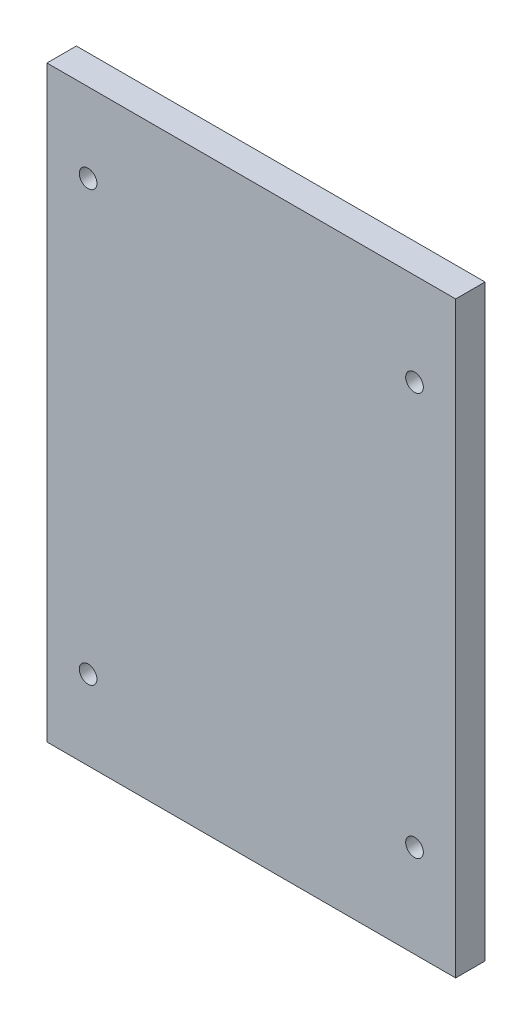
SolidWorks part; units mm, degrees
material "PBT Общее назначение"
ref_plane "Спереди" through (0, 0, 0) normal (0, 0, 1) x (1, 0, 0)
ref_plane "Сверху" through (0, 0, 0) normal (0, 1, 0) x (1, 0, 0)
ref_plane "Справа" through (0, 0, 0) normal (1, 0, 0) x (0, 0, -1)
sketch "Эскиз1" plane through (0, 0, 81) normal (0, 0, 1) x (1, 0, 0)
  line L0 (2.5, -5) -> (2.5, 95)
  line L1 (-67, -5) -> (-67, 95)
  line L4 (0, 5) -> (0, 85)
  line L5 (-61, 95) -> (-86, 95)
  line L6 (-86, 95) -> (-86, -5)
  line L7 (-86, -5) -> (-61, -5)
  line L9 (2.5, 95) -> (-67, 95)
  line L11 (-67, -5) -> (2.5, -5)
  circle A0 centre (-60, 8.5) radius 1.5 construction
  circle A1 centre (-60, 8.5) radius 1.5
  arc A2 (-61, 95) -> (0, 85) centre (0, 276.05) ccw
  arc A3 (0, 5) -> (-61, -5) centre (0, -186.05) ccw
  circle A5 centre (-60, 81.5) radius 1.5
  circle A6 centre (-60, 81.5) radius 1.5
  circle A7 centre (-4.5, 79.25) radius 1.5
  circle A8 centre (-4.5, 79.25) radius 1.5
  circle A9 centre (-4.5, 10.75) radius 1.5
  circle A10 centre (-4.5, 10.75) radius 1.5
  dimension "D5" = 7
  dimension "D6" = 7
  dimension "D2" = 0
  dimension "D1" = 0
  dimension "D3" = 0
  dimension "D4" = 0
extrude "Бобышка-Вытянуть1" add sketch "Эскиз1" against normal blind 5
